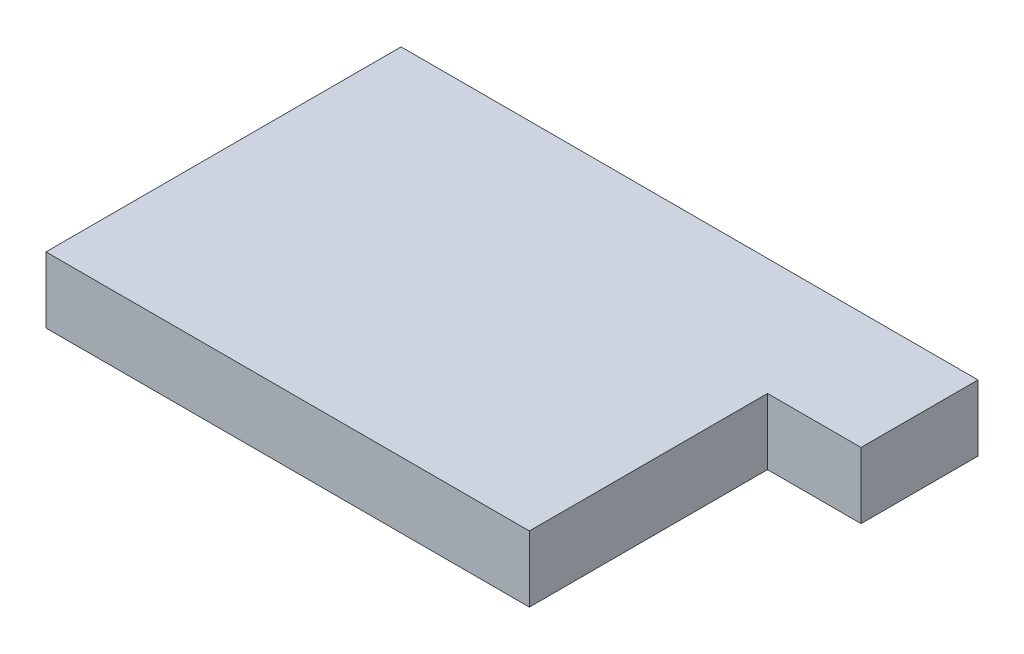
SolidWorks part; units mm, degrees
ref_plane "Front Plane" through (0, 0, 0) normal (0, 0, 1) x (1, 0, 0)
ref_plane "Top Plane" through (0, 0, 0) normal (0, 1, 0) x (1, 0, 0)
ref_plane "Right Plane" through (0, 0, 0) normal (1, 0, 0) x (0, 0, -1)
sketch "Sketch1" plane through (0, 0, 0) normal (0, 1, 0) x (1, 0, 0)
  line L1 (-139.55, 102.515) -> (139.55, 102.515)
  line L2 (-139.55, 102.515) -> (-139.55, -102.515)
  line L3 (-139.55, -102.515) -> (139.55, -102.515)
  line L4 (139.55, 34.985) -> (139.55, -102.515)
  line L5 (-139.55, 102.515) -> (139.55, -102.515) construction
  line L6 (-139.55, -102.515) -> (139.55, 102.515) construction
  line L7 (139.55, 102.515) -> (193.55, 102.515)
  line L9 (139.55, 34.985) -> (193.55, 34.985)
  line L10 (193.55, 102.515) -> (193.55, 34.985)
  point P0 (0, 0)
  point P9 (0, 0)
  dimension "D1" = 205.03
  dimension "D2" = 279.1
  dimension "D3" = 54
  dimension "D4" = 67.53
extrude "Boss-Extrude1" add sketch "Sketch1" along normal blind 38.1
